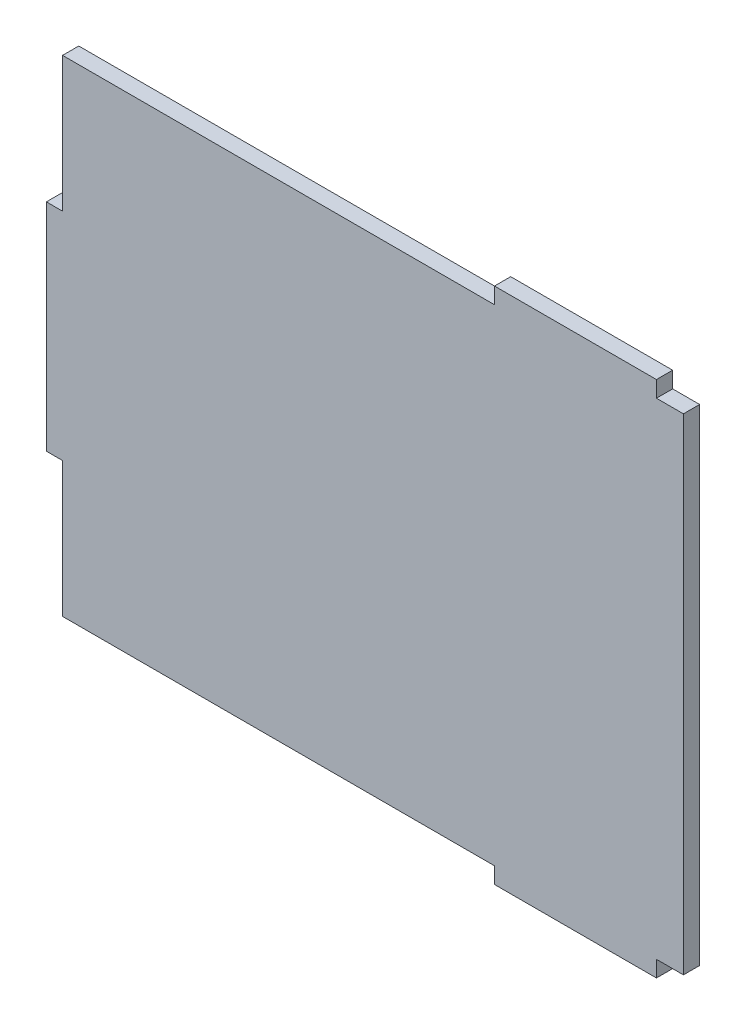
SolidWorks part; units mm, degrees
ref_plane "Front Plane" through (0, 0, 0) normal (0, 0, 1) x (1, 0, 0)
ref_plane "Top Plane" through (0, 0, 0) normal (0, 1, 0) x (1, 0, 0)
ref_plane "Right Plane" through (0, 0, 0) normal (1, 0, 0) x (0, 0, -1)
sketch "Sketch1" plane through (0, 0, 0) normal (0, 0, 1) x (1, 0, 0)
  line L0 (-57.5, -20) -> (-57.5, -45)
  line L1 (57.5, 45) -> (52.5, 45)
  line L2 (57.5, 45) -> (57.5, -45)
  line L3 (57.5, -45) -> (52.5, -45)
  line L4 (-57.5, 45) -> (-57.5, 20)
  line L7 (-60.5, -20) -> (-57.5, -20)
  line L8 (-60.5, -20) -> (-60.5, 20)
  line L9 (-60.5, 20) -> (-57.5, 20)
  line L13 (22.5, -48) -> (52.5, -48)
  line L14 (22.5, -48) -> (22.5, -45)
  line L15 (22.5, 48) -> (52.5, 48)
  line L16 (52.5, -48) -> (52.5, -45)
  line L19 (22.5, 45) -> (22.5, 48)
  line L23 (52.5, 45) -> (52.5, 48)
  line L25 (22.5, -45) -> (-57.5, -45)
  line L26 (22.5, 45) -> (-57.5, 45)
  point P0 (0, 0)
  point P16 (0, 0)
  point P17 (0, 0)
  dimension "D1" = 115
  dimension "D2" = 90
  dimension "D4" = 40
  dimension "D5" = 96
  dimension "D6" = 30
extrude "Boss-Extrude1" add sketch "Sketch1" along normal blind 3
